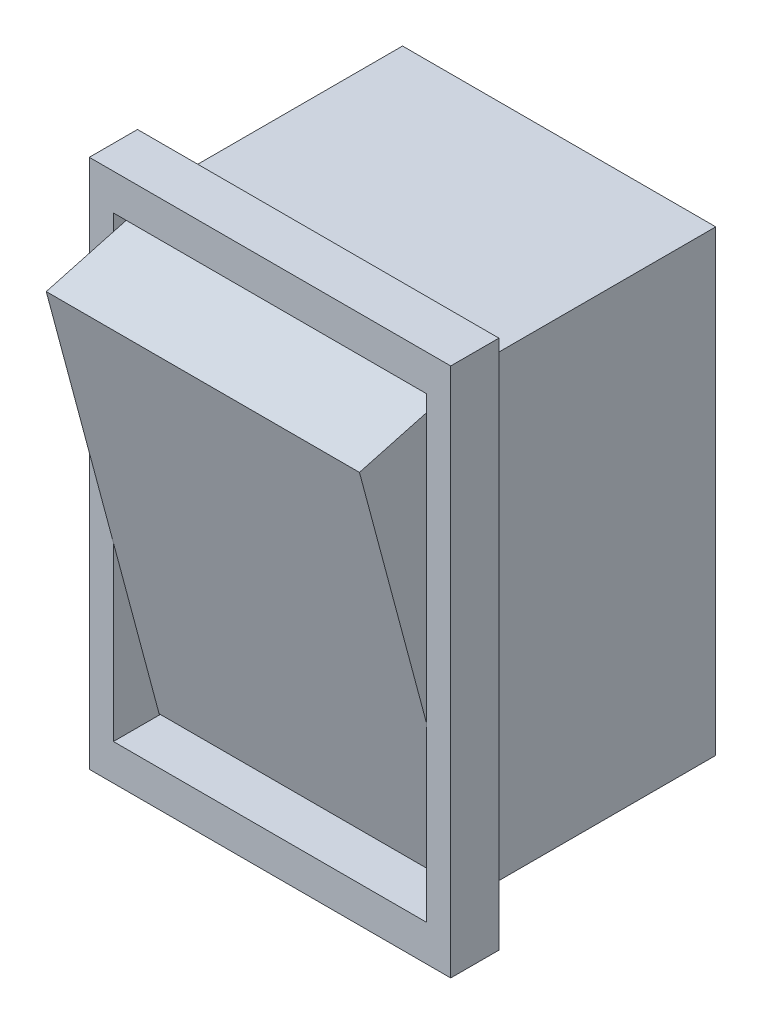
SolidWorks part; units mm, degrees
ref_plane "Front Plane" through (0, 0, 0) normal (0, 0, 1) x (1, 0, 0)
ref_plane "Top Plane" through (0, 0, 0) normal (0, 1, 0) x (1, 0, 0)
ref_plane "Right Plane" through (0, 0, 0) normal (1, 0, 0) x (0, 0, -1)
sketch "Sketch1" plane through (0, 0, 0) normal (0, 0, 1) x (1, 0, 0)
  line L1 (-6.5, -9.5) -> (6.5, -9.5)
  line L2 (-6.5, -9.5) -> (-6.5, 9.5)
  line L3 (-6.5, 9.5) -> (6.5, 9.5)
  line L4 (6.5, -9.5) -> (6.5, 9.5)
  line L5 (-6.5, -9.5) -> (6.5, 9.5) construction
  line L6 (-6.5, 9.5) -> (6.5, -9.5) construction
  point P0 (0, 0)
  dimension "D1" = 13
  dimension "D2" = 19
extrude "Boss-Extrude1" add sketch "Sketch1" along normal blind 10
sketch "Sketch2" plane through (0, 0, 10) normal (0, 0, 1) x (1, 0, 0)
  line L1 (-7.5, -11) -> (7.5, -11)
  line L2 (-7.5, -11) -> (-7.5, 11)
  line L3 (-7.5, 11) -> (7.5, 11)
  line L4 (7.5, -11) -> (7.5, 11)
  line L5 (-7.5, -11) -> (7.5, 11) construction
  line L6 (-7.5, 11) -> (7.5, -11) construction
  line L7 (6.5, -9.5) -> (-6.5, -9.5)
  line L8 (6.5, -9.5) -> (6.5, 9.5)
  line L9 (6.5, 9.5) -> (-6.5, 9.5)
  line L10 (-6.5, -9.5) -> (-6.5, 9.5)
  line L11 (6.5, -9.5) -> (-6.5, 9.5) construction
  line L12 (6.5, 9.5) -> (-6.5, -9.5) construction
  point P0 (0, 0)
  point P5 (0, 0)
  dimension "D1" = 15
  dimension "D2" = 22
extrude "Boss-Extrude2" add sketch "Sketch2" along normal blind 2
sketch "Sketch3" plane through (-6.5, 0, 0) normal (1, 0, 0) x (0, 0, -1)
  line L9 (-10.1028, 9.3379) -> (-14.7873, 8.0674)
  line L10 (-14.7873, 8.0674) -> (-10.1028, -9.45)
  line L11 (-10.1028, -9.45) -> (-10.1028, 9.3379)
  point P4 (-10.1028, 9.3379)
  point P6 (-10.316, -9.4445)
  point P7 (-10.1028, -9.45)
  point P8 (-14.7873, 8.0674)
extrude "Boss-Extrude11" add sketch "Sketch3" along normal up to surface (13 mm away) contours L9 L10 L11 up to face at (6.5, 0, 11)
